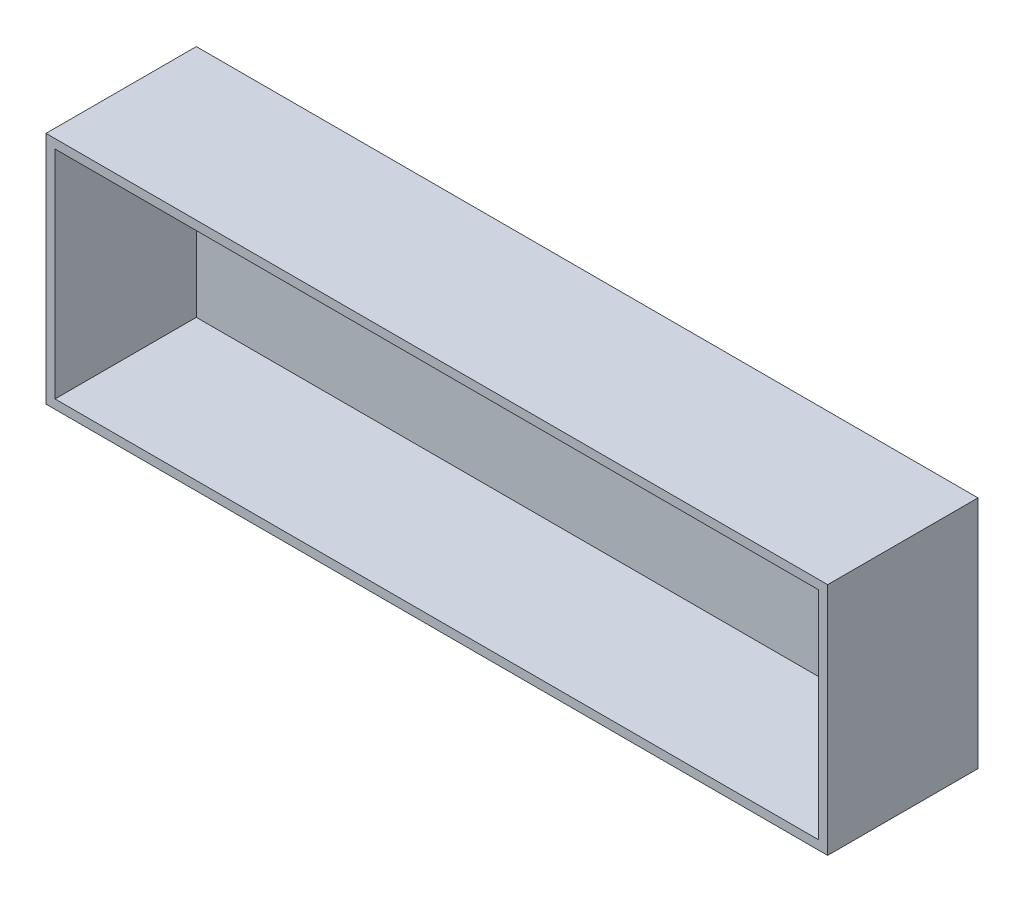
SolidWorks part; units mm, degrees
material "玻璃"
ref_plane "前视基准面" through (0, 0, 0) normal (0, 0, 1) x (1, 0, 0)
ref_plane "上视基准面" through (0, 0, 0) normal (0, 1, 0) x (1, 0, 0)
ref_plane "右视基准面" through (0, 0, 0) normal (1, 0, 0) x (0, 0, -1)
sketch "草图1" plane through (0, 0, 0) normal (0, 0, 1) x (1, 0, 0)
  line L1 (-130, 39) -> (130, 39)
  line L2 (-130, 39) -> (-130, -39)
  line L3 (-130, -39) -> (130, -39)
  line L4 (130, 39) -> (130, -39)
  line L5 (-130, 39) -> (130, -39) construction
  line L6 (-130, -39) -> (130, 39) construction
  point P0 (0, 0)
  dimension "D1" = 260
  dimension "D2" = 78
extrude "凸台-拉伸1" add sketch "草图1" along normal blind 50
shell "抽壳1" thickness 3
